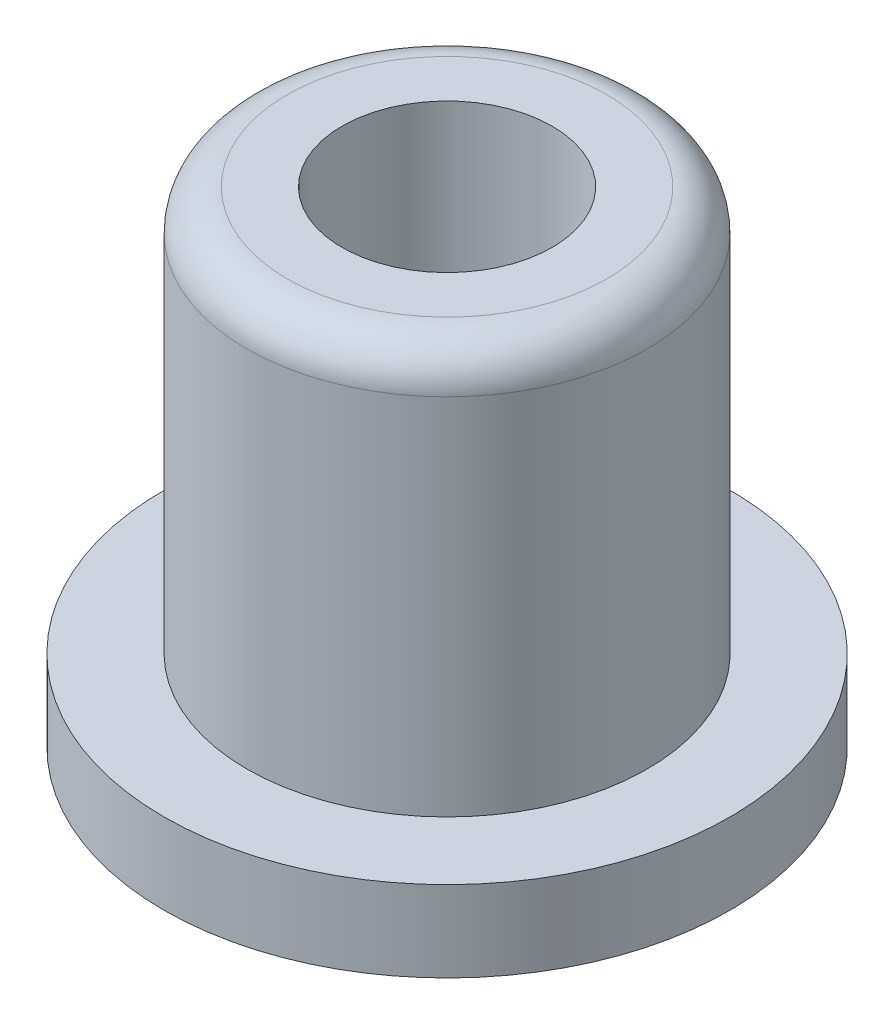
SolidWorks part; units mm, degrees
ref_plane "Front Plane" through (0, 0, 0) normal (0, 0, 1) x (1, 0, 0)
ref_plane "Top Plane" through (0, 0, 0) normal (0, 1, 0) x (1, 0, 0)
ref_plane "Right Plane" through (0, 0, 0) normal (1, 0, 0) x (0, 0, -1)
sketch "Sketch1" plane through (0, 0, 0) normal (0, 1, 0) x (1, 0, 0)
  circle A0 centre (0, 0) radius 7
  dimension "D1" = 14
extrude "Boss-Extrude1" add sketch "Sketch1" along normal blind 2
sketch "Sketch2" plane through (0, 2, 0) normal (0, 1, 0) x (1, 0, 0)
  circle A0 centre (0, 0) radius 4.95
  dimension "D1" = 9.9
extrude "Boss-Extrude2" add sketch "Sketch2" along normal blind 10
sketch "Sketch3" plane through (0, 0, 0) normal (0, -1, 0) x (1, 0, 0)
  circle A0 centre (0, 0) radius 2.6
  dimension "D1" = 5.2
extrude "Cut-Extrude1" cut sketch "Sketch3" against normal through all
fillet "Fillet1" radius 1 1 edges at (0, 12, 4.95)
